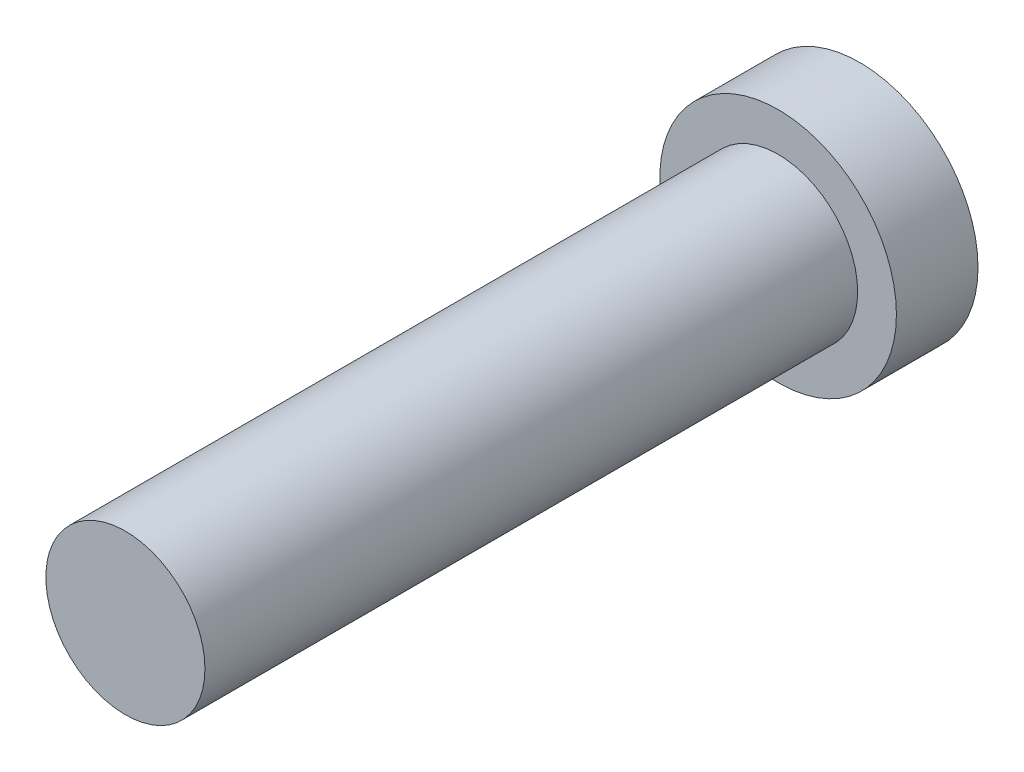
SolidWorks part; units mm, degrees
ref_plane "Front Plane" through (0, 0, 0) normal (0, 0, 1) x (1, 0, 0)
ref_plane "Top Plane" through (0, 0, 0) normal (0, 1, 0) x (1, 0, 0)
ref_plane "Right Plane" through (0, 0, 0) normal (1, 0, 0) x (0, 0, -1)
sketch "Sketch1" plane through (0, 0, 0) normal (0, 0, 1) x (1, 0, 0)
  circle A0 centre (0, 0) radius 2.9
  dimension "D1" = 5.8
extrude "Boss-Extrude1" add sketch "Sketch1" along normal blind 2
sketch "Sketch2" plane through (0, 0, 2) normal (0, 0, 1) x (1, 0, 0)
  circle A0 centre (0, 0) radius 1.95
  dimension "D1" = 3.9
extrude "Boss-Extrude2" add sketch "Sketch2" along normal blind 16
